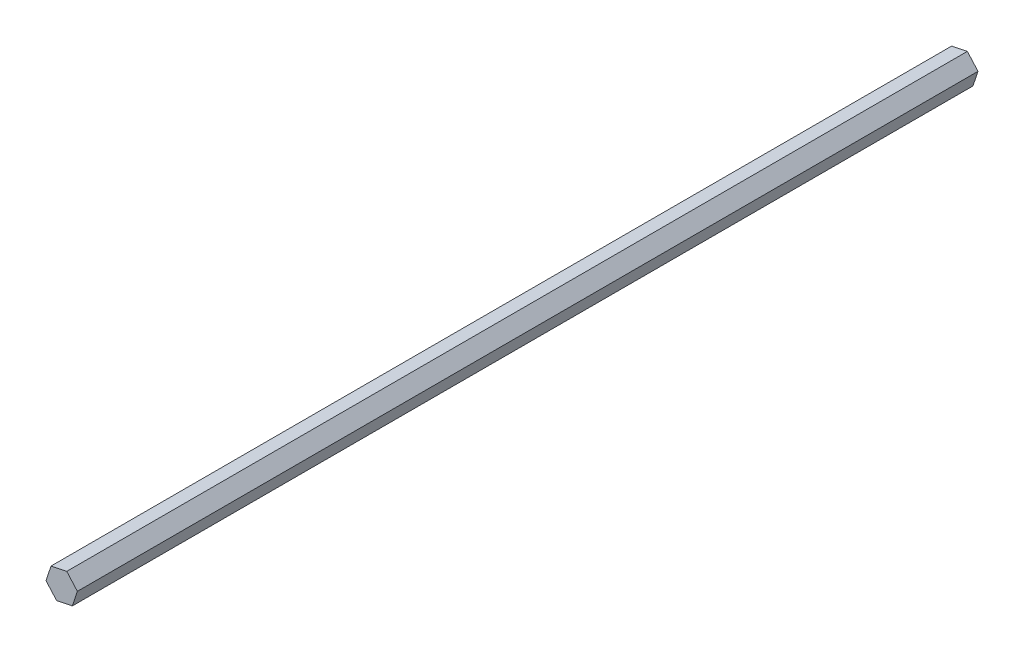
SolidWorks part; units mm, degrees
material "7075-O (SS)"
ref_plane "Front Plane" through (0, 0, 0) normal (0, 0, 1) x (1, 0, 0)
ref_plane "Top Plane" through (0, 0, 0) normal (0, 1, 0) x (1, 0, 0)
ref_plane "Right Plane" through (0, 0, 0) normal (1, 0, 0) x (0, 0, -1)
sketch "Sketch1" plane through (0, 0, 0) normal (0, 0, 1) x (1, 0, 0)
  line L1 (4.8713, -5.4803) -> (7.1817, 1.4786)
  line L2 (7.1817, 1.4786) -> (2.3104, 6.9588)
  line L3 (2.3104, 6.9588) -> (-4.8713, 5.4803)
  line L4 (-4.8713, 5.4803) -> (-7.1817, -1.4786)
  line L5 (-7.1817, -1.4786) -> (-2.3104, -6.9588)
  line L6 (-2.3104, -6.9588) -> (4.8713, -5.4803)
  circle A0 centre (0, 0) radius 6.35 construction
  dimension "D1" = 12.7
extrude "Boss-Extrude1" add sketch "Sketch1" along normal blind 412.242
